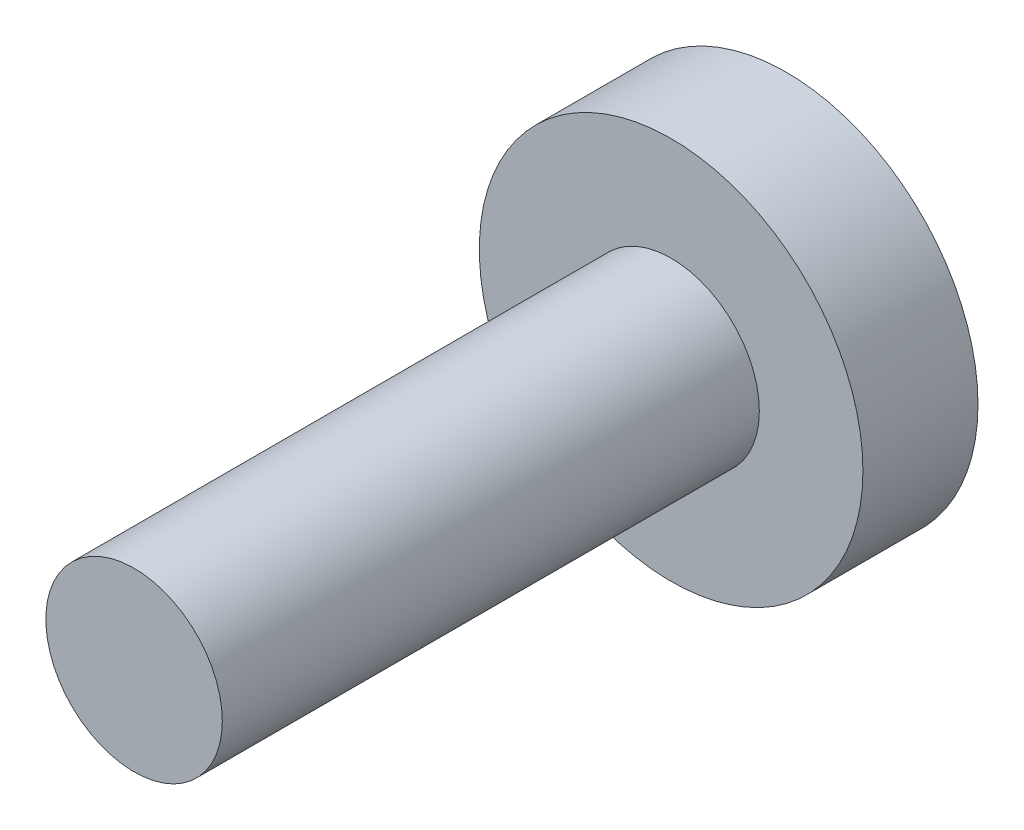
SolidWorks part; units mm, degrees
ref_plane "Front Plane" through (0, 0, 0) normal (0, 0, 1) x (1, 0, 0)
ref_plane "Top Plane" through (0, 0, 0) normal (0, 1, 0) x (1, 0, 0)
ref_plane "Right Plane" through (0, 0, 0) normal (1, 0, 0) x (0, 0, -1)
sketch "Sketch1" plane through (0, 0, 0) normal (0, 0, 1) x (1, 0, 0)
  circle A0 centre (0, 0) radius 2.921
  dimension "D1" = 5.842
extrude "Boss-Extrude1" add sketch "Sketch1" along normal blind 17.78
sketch "Sketch2" plane through (0, 0, 0) normal (0, 0, 1) x (1, 0, 0)
  circle A0 centre (0, 0) radius 6.35
  dimension "D1" = 12.7
extrude "Boss-Extrude2" add sketch "Sketch2" against normal blind 3.81
